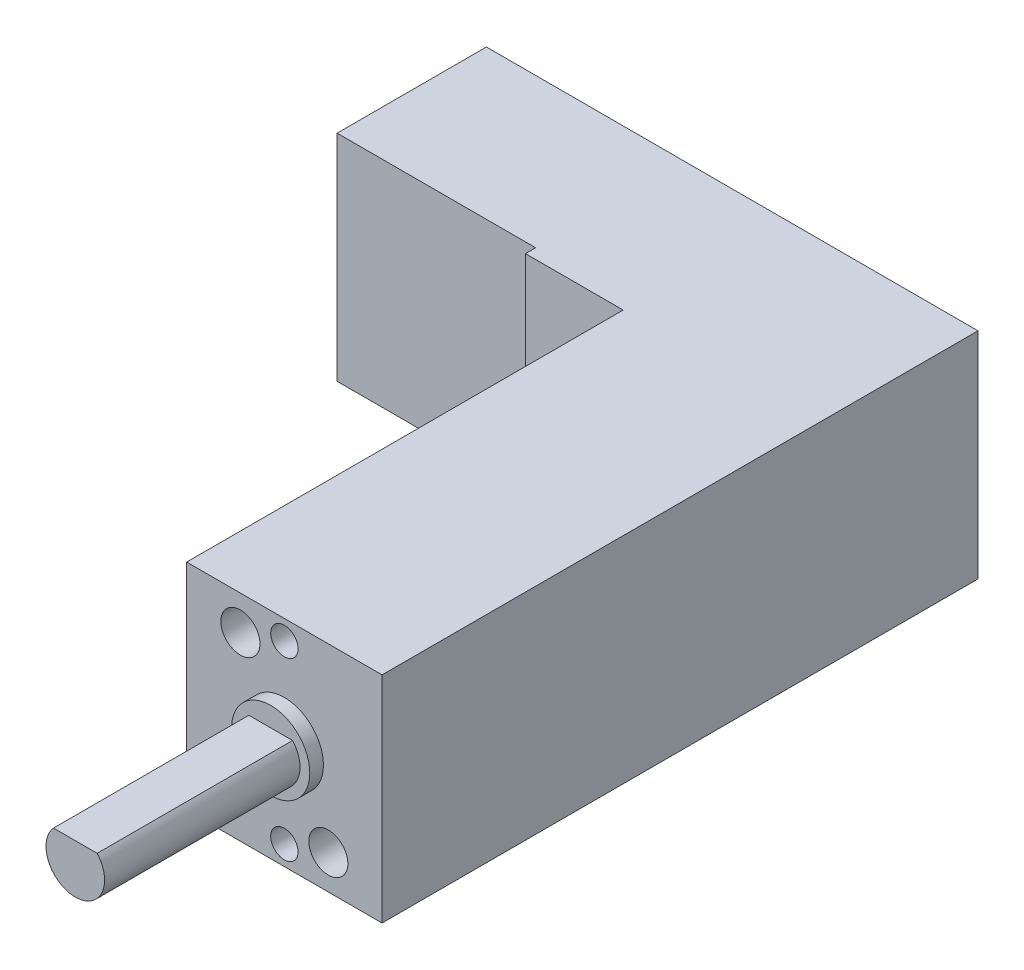
SolidWorks part; units mm, degrees
material "Default"
ref_plane "Top" through (0, 0, 0) normal (0, 0, 1) x (1, 0, 0)
ref_plane "Right" through (0, 0, 0) normal (0, 1, 0) x (1, 0, 0)
ref_plane "Front" through (0, 0, 0) normal (1, 0, 0) x (0, 0, -1)
sketch "Sketch1" plane through (0, 0, 0) normal (0, 0, 1) x (1, 0, 0)
  line L0 (-263.838, 0) -> (344.331, 0) construction
  line L1 (0, 2.0741) -> (0, 382.1797) construction
  line L2 (-7.5, 5.5) -> (7.5, 5.5)
  line L3 (7.5, 5.5) -> (7.5, -5.5)
  line L4 (-7.5, 5.5) -> (-7.5, -5.5)
  line L7 (-7.5, -5.5) -> (7.5, -5.5)
  point P10 (0, 5.5)
  dimension "D1" = 7.5
  dimension "D2" = 5.5
extrude "Boss-Extrude1" add sketch "Sketch1" along normal blind 21.5
sketch "Sketch2" plane through (0, 0, 21.5) normal (0, 0, 1) x (1, 0, 0)
  line L0 (7.5, 5.5) -> (-2.5, 5.5)
  line L1 (-2.5, -5.5) -> (-2.5, 5.5)
  line L3 (-7.5, -5.5) -> (7.5, -5.5) construction
  line L5 (7.5, -5.5) -> (7.5, 5.5)
  line L6 (-2.5, -5.5) -> (7.5, -5.5)
  line L7 (2.5, 5.5) -> (2.5, -5.5) construction
  line L8 (7.5, 0) -> (-2.5, 0) construction
  dimension "D1" = 10
extrude "Boss-Extrude2" add sketch "Sketch2" along normal blind 9
sketch "Sketch3" plane through (0, 0, 30.5) normal (0, 0, 1) x (1, 0, 0)
  line L0 (2.5, 5.5) -> (2.5, -5.5) construction
  line L1 (7.5, 5.5) -> (-2.5, 5.5) construction
  line L2 (-2.5, -5.5) -> (7.5, -5.5) construction
  line L3 (7.5, 0) -> (-2.5, 0) construction
  line L4 (7.5, -5.5) -> (7.5, 5.5) construction
  line L5 (-2.5, 5.5) -> (-2.5, -5.5) construction
  circle A0 centre (2.5, 0) radius 2
  dimension "D1" = 4
extrude "Boss-Extrude3" add sketch "Sketch3" along normal blind 0.7
sketch "Sketch4" plane through (0, 0, 31.2) normal (0, 0, 1) x (1, 0, 0)
  line L0 (2.5, 5.5) -> (2.5, -5.5) construction
  line L1 (7.5, 5.5) -> (-2.5, 5.5) construction
  line L2 (-2.5, -5.5) -> (7.5, -5.5) construction
  line L3 (7.5, 0) -> (-2.5, 0) construction
  line L4 (7.5, -5.5) -> (7.5, 5.5) construction
  line L5 (-2.5, 5.5) -> (-2.5, -5.5) construction
  circle A0 centre (2.5, 0) radius 1.5
extrude "Boss-Extrude4" add sketch "Sketch4" along normal blind 10
sketch "Sketch5" plane through (0, 0, 41.2) normal (0, 0, 1) x (1, 0, 0)
  line L0 (-2.5, 0) -> (7.5, 0) construction
  line L1 (-2.5, 5.5) -> (-2.5, -5.5) construction
  line L2 (7.5, -5.5) -> (7.5, 5.5) construction
  line L3 (2.5, 5.5) -> (2.5, -5.5) construction
  line L4 (7.5, 5.5) -> (-2.5, 5.5) construction
  line L5 (-2.5, -5.5) -> (7.5, -5.5) construction
  line L6 (1.382, 1) -> (3.618, 1)
  line L7 (-1.56, -1.5) -> (6.7819, -1.5) construction
  circle A2 centre (2.5, 0) radius 1.5 construction
  circle A3 centre (2.5, 0) radius 1.5 construction
  arc A4 (3.618, 1) -> (1.382, 1) centre (2.5, 0) ccw
  dimension "D1" = 2.5
extrude "Cut-Extrude1" cut sketch "Sketch5" against normal blind 10
sketch "Sketch6" plane through (0, 0, 30.5) normal (0, 0, 1) x (1, 0, 0)
  line L0 (2.5, 5.5) -> (2.5, -5.5) construction
  line L1 (7.5, 5.5) -> (-2.5, 5.5) construction
  line L2 (-2.5, -5.5) -> (7.5, -5.5) construction
  line L3 (7.5, 0) -> (-2.5, 0) construction
  line L4 (7.5, -5.5) -> (7.5, 5.5) construction
  line L5 (-2.5, 5.5) -> (-2.5, -5.5) construction
  circle A0 centre (2.5, 4.5) radius 0.7
  circle A1 centre (2.5, -4.5) radius 0.7
  circle A2 centre (4.75, -3.75) radius 1
  circle A3 centre (0.25, 3.75) radius 1
  dimension "D1" = 4.5
  dimension "D2" = 2
  dimension "D3" = 1.4
  dimension "D4" = 2
  dimension "D5" = 4.5
  dimension "D6" = 7.5
  dimension "D7" = 7.5
  dimension "D8" = 2.25
extrude "Cut-Extrude2" cut sketch "Sketch6" against normal blind 3
sketch "Sketch7" plane through (-7.5, 0, 0) normal (-1, 0, 0) x (0, 0, 1)
  line L0 (7.64, 5.5) -> (7.64, -5.5)
  line L1 (21.5, 5.5) -> (0, 5.5) construction
  line L2 (21.5, -5.5) -> (0, -5.5) construction
  line L4 (30.5, 5.5) -> (30.5, -5.5) construction
  line L5 (7.64, 5.5) -> (0, 5.5)
  line L6 (0, 5.5) -> (0, -5.5)
  line L7 (0, -5.5) -> (7.64, -5.5)
  dimension "D1" = 22.86
extrude "Boss-Extrude5" add sketch "Sketch7" along normal blind 10.16
sketch "Sketch8" plane through (0, -5.5, 0) normal (0, -1, 0) x (1, 0, 0)
  line L1 (-7.5, 21.5) -> (-2.5, 21.5)
  line L2 (-7.5, 21.5) -> (-7.5, 8.16)
  line L3 (-7.5, 8.16) -> (-2.5, 8.16)
  line L4 (-2.5, 21.5) -> (-2.5, 8.16)
extrude "Cut-Extrude3" cut sketch "Sketch8" against normal up to surface (11 mm away) up to face at (-5.04, 5.5, 14.91)
